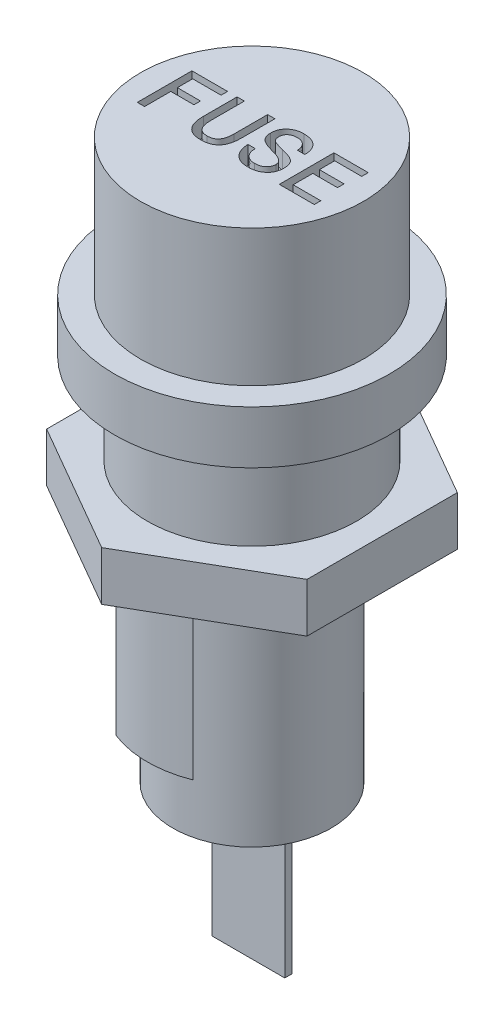
SolidWorks part; units mm, degrees
ref_plane "Front Plane" through (0, 0, 0) normal (0, 0, 1) x (1, 0, 0)
ref_plane "Top Plane" through (0, 0, 0) normal (0, 1, 0) x (1, 0, 0)
ref_plane "Right Plane" through (0, 0, 0) normal (1, 0, 0) x (0, 0, -1)
sketch "Sketch1" plane through (0, 0, 0) normal (0, 1, 0) x (1, 0, 0)
  circle A0 centre (0, 0) radius 5.75
  dimension "D1" = 11.5
extrude "Boss-Extrude1" add sketch "Sketch1" along normal blind 7.7
sketch "Sketch2" plane through (0, 0, 0) normal (0, -1, 0) x (1, 0, 0)
  circle A0 centre (0, 0) radius 4.35
  dimension "D1" = 8.7
extrude "Boss-Extrude2" add sketch "Sketch2" along normal blind 12.6
sketch "Sketch3" plane through (0, 7.7, 0) normal (0, 1, 0) x (1, 0, 0)
  circle A0 centre (0, 0) radius 7.55
  dimension "D1" = 15.1
extrude "Boss-Extrude3" add sketch "Sketch3" along normal blind 2.9
sketch "Sketch4" plane through (0, 10.6, 0) normal (0, 1, 0) x (1, 0, 0)
  circle A0 centre (0, 0) radius 6.125
  dimension "D1" = 12.25
extrude "Boss-Extrude4" add sketch "Sketch4" along normal blind 7.5
sketch "Sketch5" plane through (0, 18.1, 0) normal (0, 1, 0) x (1, 0, 0)
  line L0 (-5.9385, -1.5) -> (5.9385, -1.5) construction
  circle A0 centre (0, 0) radius 6.125 construction
  text T0 "FUSE" font "Monospac821 BT" height 3
  dimension "D1" = 1.5
extrude "Cut-Extrude1" cut sketch "Sketch5" against normal blind 1
sketch "Sketch6" plane through (0, 0, 0) normal (0, -1, 0) x (1, 0, 0)
  line L1 (-7.15, 4.1281) -> (-7.15, -4.1281)
  line L2 (-7.15, -4.1281) -> (0, -8.2561)
  line L3 (0, -8.2561) -> (7.15, -4.1281)
  line L4 (7.15, -4.1281) -> (7.15, 4.1281)
  line L5 (7.15, 4.1281) -> (0, 8.2561)
  line L6 (0, 8.2561) -> (-7.15, 4.1281)
  circle A0 centre (0, 0) radius 5.75
  circle A1 centre (0, 0) radius 5.75 construction
  circle A2 centre (0, 0) radius 7.15 construction
  dimension "D1" = 14.3
extrude "Boss-Extrude5" add sketch "Sketch6" against normal blind 2.7 separate body
sketch "Sketch7" plane through (0, -12.6, 0) normal (0, -1, 0) x (1, 0, 0)
  line L1 (-2, -0.2) -> (2, -0.2)
  line L2 (-2, -0.2) -> (-2, 0.2)
  line L3 (-2, 0.2) -> (2, 0.2)
  line L4 (2, -0.2) -> (2, 0.2)
  line L5 (-2, -0.2) -> (2, 0.2) construction
  line L6 (-2, 0.2) -> (2, -0.2) construction
  point P0 (0, 0)
  dimension "D1" = 4
  dimension "D2" = 0.4
extrude "Boss-Extrude6" add sketch "Sketch7" along normal blind 8.2
sketch "Sketch8" plane through (0, 0, 0) normal (0, -1, 0) x (1, 0, 0)
  line L0 (-2.1071, 5.35) -> (2.1071, 5.35)
  line L1 (0, 5.75) -> (0, 5.35) construction
  circle A0 centre (0, 0) radius 5.75 construction
  circle A1 centre (0, 0) radius 5.75 construction
  arc A2 (2.1071, 5.35) -> (-2.1071, 5.35) centre (0, 0) ccw
  dimension "D1" = 0.4
extrude "Boss-Extrude7" add sketch "Sketch8" along normal blind 8.75
